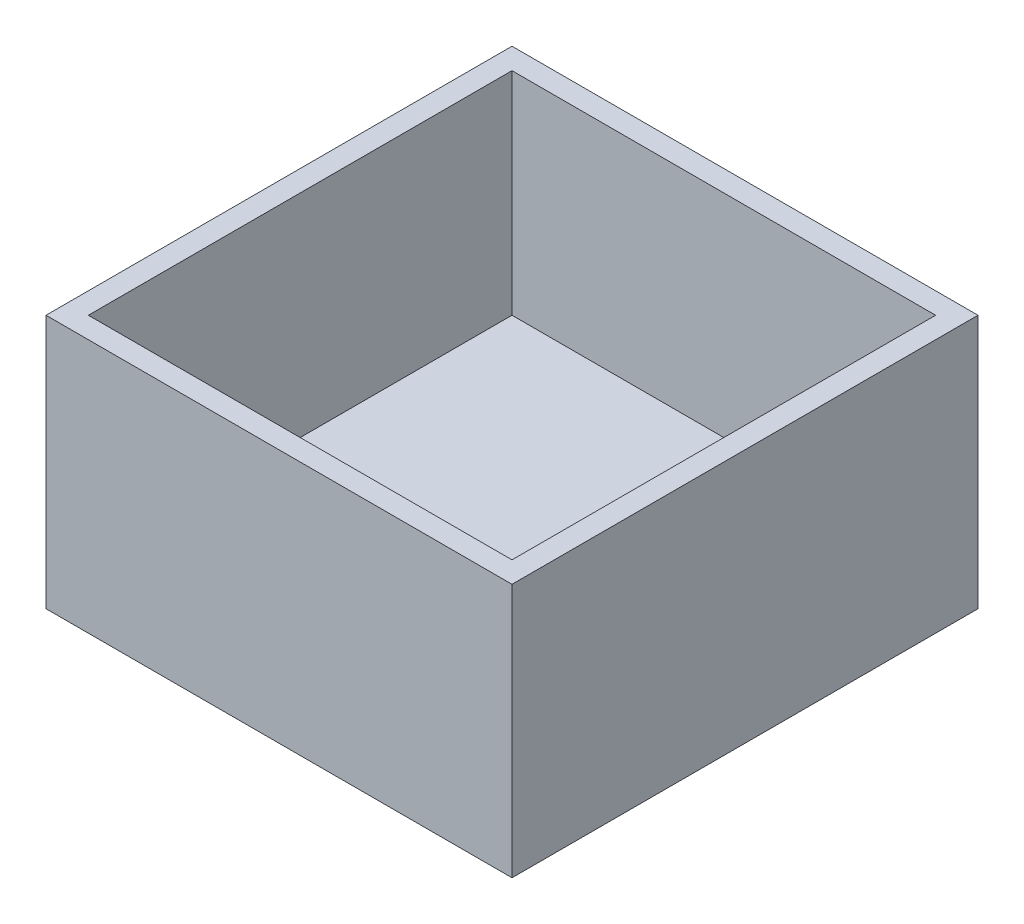
SolidWorks part; units mm, degrees
ref_plane "Front Plane" through (0, 0, 0) normal (0, 0, 1) x (1, 0, 0)
ref_plane "Top Plane" through (0, 0, 0) normal (0, 1, 0) x (1, 0, 0)
ref_plane "Right Plane" through (0, 0, 0) normal (1, 0, 0) x (0, 0, -1)
sketch "Sketch2" plane through (0, 0, 0) normal (0, 1, 0) x (1, 0, 0)
  line L1 (-10, -10) -> (10, -10)
  line L2 (-10, -10) -> (-10, 10)
  line L3 (-10, 10) -> (10, 10)
  line L4 (10, -10) -> (10, 10)
  line L5 (-10, -10) -> (10, 10) construction
  line L6 (-10, 10) -> (10, -10) construction
  line L7 (-11, -11) -> (11, -11)
  line L8 (-11, -11) -> (-11, 11)
  line L9 (-11, 11) -> (11, 11)
  line L10 (11, -11) -> (11, 11)
  line L11 (-11, -11) -> (11, 11) construction
  line L12 (-11, 11) -> (11, -11) construction
  point P0 (0, 0)
  point P6 (0, 0)
  dimension "D1" = 20
  dimension "D2" = 20
  dimension "D3" = 22
  dimension "D4" = 22
extrude "Boss-Extrude1" add sketch "Sketch2" along normal blind 12
sketch "Sketch3" plane through (0, 0, 0) normal (0, 1, 0) x (1, 0, 0)
  line L1 (-10, -10) -> (10, -10)
  line L2 (-10, -10) -> (-10, 10)
  line L3 (-10, 10) -> (10, 10)
  line L4 (10, -10) -> (10, 10)
  line L5 (-10, -10) -> (10, 10) construction
  line L6 (-10, 10) -> (10, -10) construction
  point P0 (0, 0)
extrude "Boss-Extrude2" add sketch "Sketch3" along normal blind 2
